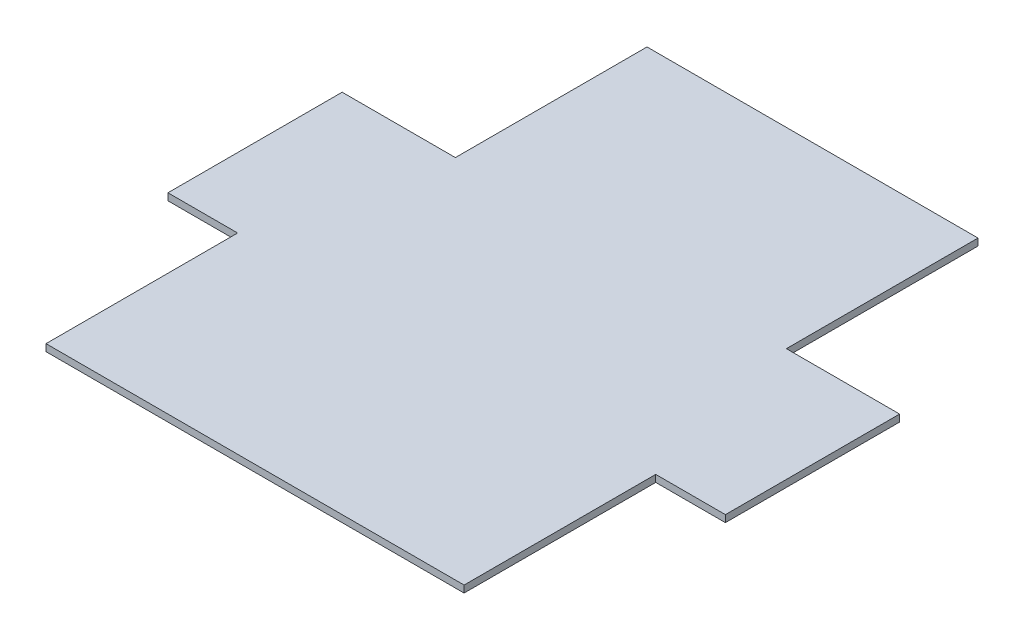
SolidWorks part; units mm, degrees
material "Nylon 6/10"
ref_plane "Front Plane" through (0, 0, 0) normal (0, 0, 1) x (1, 0, 0)
ref_plane "Top Plane" through (0, 0, 0) normal (0, 1, 0) x (1, 0, 0)
ref_plane "Right Plane" through (0, 0, 0) normal (1, 0, 0) x (0, 0, -1)
sketch "Sketch1" plane through (0, 0, 0) normal (0, 1, 0) x (1, 0, 0)
  line L1 (-47.5, 80) -> (47.5, 80)
  line L2 (-47.5, 80) -> (-47.5, 25)
  line L3 (-60, -80) -> (60, -80)
  line L4 (47.5, 80) -> (47.5, 25)
  line L6 (-80, 25) -> (-47.5, 25)
  line L7 (-80, 25) -> (-80, -25)
  line L8 (-80, -25) -> (-60, -25)
  line L9 (80, 25) -> (80, -25)
  line L10 (60, -25) -> (80, -25)
  line L11 (47.5, 25) -> (80, 25)
  line L12 (-60, -25) -> (-60, -80)
  line L13 (60, -25) -> (60, -80)
  point P4 (0, 80)
  point P10 (0, -80)
  dimension "D1" = 160
  dimension "D2" = 120
  dimension "D3" = 160
  dimension "D4" = 50
  dimension "D5" = 55
  dimension "D6" = 80
  dimension "D7" = 95
extrude "Extrude1" add sketch "Sketch1" along normal blind 2
